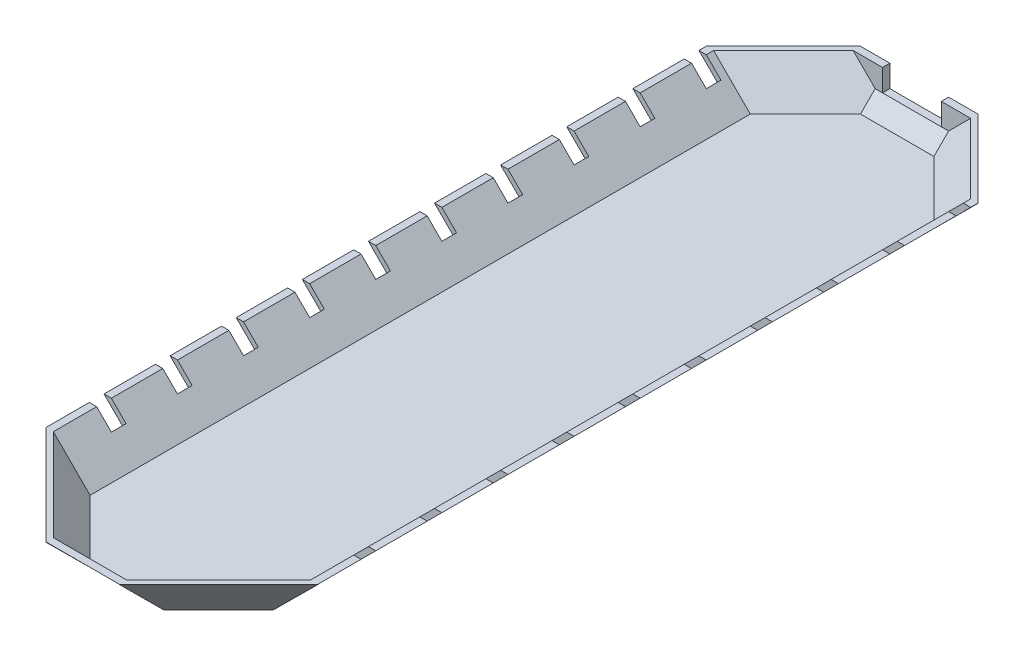
SolidWorks part; units mm, degrees
ref_plane "Front Plane" through (0, 0, 0) normal (0, 0, 1) x (1, 0, 0)
ref_plane "Top Plane" through (0, 0, 0) normal (0, 1, 0) x (1, 0, 0)
ref_plane "Right Plane" through (0, 0, 0) normal (1, 0, 0) x (0, 0, -1)
sketch "Sketch1" plane through (0, 0, 0) normal (0, 1, 0) x (1, 0, 0)
  line L0 (0, -262.2479) -> (0, 262.2479) construction
  line L2 (62.4979, -224.75) -> (62.4979, 224.75)
  line L4 (-62.4979, -224.75) -> (-62.4979, 224.75)
  line L5 (62.4979, -224.75) -> (-62.4979, 224.75) construction
  line L6 (62.4979, 224.75) -> (-62.4979, -224.75) construction
  line L7 (-25, 262.2479) -> (25, 262.2479)
  line L8 (-25, -262.2479) -> (25, -262.2479)
  line L9 (-62.4979, 224.75) -> (-25, 262.2479)
  line L10 (25, 262.2479) -> (62.4979, 224.75)
  line L11 (25, -262.2479) -> (62.4979, -224.75)
  line L12 (-62.4979, -224.75) -> (-25, -262.2479)
  point P0 (0, 0)
  dimension "D1" = 449.5
  dimension "D2" = 50
  dimension "D3" = 25
  dimension "D4" = 50
  dimension "D5" = 25
  dimension "D6" = 53.03
  dimension "D8" = 53.03
extrude "Boss-Extrude1" add sketch "Sketch1" along normal blind 5
sketch "Sketch2" plane through (62.4979, 0, 0) normal (1, 0, 0) x (0, 0, -1)
  line L0 (0, 5) -> (0, 0) construction
  line L1 (-224.75, 5) -> (224.75, 5) construction
ref_plane "Plane1" through (0, 0, 0) normal (0, 0, 1) x (0, -1, 0)
sketch "Sketch3" plane through (0, 0, 0) normal (0, 0, 1) x (0, -1, 0)
  line L0 (0, 62.4979) -> (-5, 62.4979)
  line L1 (-5, 62.4979) -> (-30, 87.4979)
  line L2 (-30, 87.4979) -> (-30, 92.4979)
  line L3 (-30, 92.4979) -> (0, 62.4979)
  line L4 (-5, 62.4979) -> (-30, 62.4979) construction
  line L5 (-30, 62.4979) -> (-30, 87.4979) construction
  line L6 (0, 0) -> (-58.1872, 0) construction
  line L7 (-30, -87.4979) -> (-30, -92.4979)
  line L8 (-5, -62.4979) -> (-30, -87.4979)
  line L9 (0, -62.4979) -> (-5, -62.4979)
  line L10 (-30, -92.4979) -> (0, -62.4979)
  dimension "D1" = 5
  dimension "D2" = 25
extrude "Boss-Extrude2" add sketch "Sketch3" along normal mid plane 449.5
sketch "Sketch5" plane through (0, 0, 262.2479) normal (0, 0, 1) x (1, 0, 0)
  line L0 (0, 5) -> (0, 0) construction
  line L1 (-25, 5) -> (25, 5) construction
ref_plane "Plane2" through (0, 0, 0) normal (-1, 0, 0) x (0, -1, 0)
sketch "Sketch6" plane through (0, 0, 0) normal (-1, 0, 0) x (0, -1, 0)
  line L0 (0, 262.2479) -> (-30, 292.2479)
  line L1 (-30, 292.2479) -> (-30, 287.2479)
  line L2 (-30, 287.2479) -> (-5, 262.2479)
  line L3 (-5, 262.2479) -> (0, 262.2479)
  line L4 (-5, 262.2479) -> (-30, 262.2479) construction
  line L5 (-30, 262.2479) -> (-30, 287.2479) construction
  line L6 (-5, -262.2479) -> (-15, -262.2479) construction
  line L7 (0, -262.2479) -> (-15, -277.2479)
  line L8 (-15, -277.2479) -> (-15, -272.2479)
  line L9 (-15, -272.2479) -> (-5, -262.2479)
  line L10 (-5, -262.2479) -> (0, -262.2479)
  line L11 (-15, -262.2479) -> (-15, -272.2479) construction
  dimension "D1" = 25
  dimension "D2" = 5
  dimension "D3" = 10
  dimension "D4" = 5
extrude "Boss-Extrude3" add sketch "Sketch6" along normal mid plane 50
sketch "Sketch7" plane through (0, 15, 0) normal (0, 1, 0) x (1, 0, 0)
  line L0 (-25, 272.2479) -> (25, 272.2479) construction
  line L1 (-25, 277.2479) -> (-20, 277.2479)
  line L2 (-25, 277.2479) -> (-25, 272.2479)
  line L3 (-25, 272.2479) -> (-20, 272.2479)
  line L4 (-20, 277.2479) -> (-20, 272.2479)
  line L6 (25, 277.2479) -> (20, 277.2479)
  line L7 (25, 277.2479) -> (25, 272.2479)
  line L8 (25, 272.2479) -> (20, 272.2479)
  line L9 (20, 277.2479) -> (20, 272.2479)
  dimension "D1" = 5
  dimension "D2" = 5
extrude "Boss-Extrude5" add sketch "Sketch7" along normal blind 15
sketch "Sketch9" plane through (-143.6239, 0, -143.6239) normal (-0.7071, 0, -0.7071) x (-0.7071, 0, 0.7071)
  line L0 (-141.2446, 5) -> (-141.2446, 0) construction
  line L1 (-167.7596, 5) -> (-114.7296, 5) construction
  line L2 (-167.7596, 0) -> (-114.7296, 0) construction
ref_plane "Plane3" through (99.875, 0, -99.875) normal (0.7071, 0, -0.7071) x (0, -1, 0)
sketch "Sketch10" plane through (99.875, 0, -99.875) normal (0.7071, 0, -0.7071) x (0, -1, 0)
  line L0 (0, 203.1149) -> (-30, 224.3281)
  line L1 (-30, 224.3281) -> (-30, 220.7926)
  line L2 (-30, 220.7926) -> (-5, 203.1149)
  line L3 (-5, 203.1149) -> (0, 203.1149) construction
  line L4 (-5, 203.1149) -> (0, 203.1149)
extrude "Boss-Extrude6" add sketch "Sketch10" along normal mid plane 100
sketch "Sketch11" plane through (143.6239, 0, -143.6239) normal (0.7071, 0, -0.7071) x (-0.7071, 0, -0.7071)
  line L0 (141.2446, 5) -> (141.2446, 0) construction
  line L1 (114.7296, 5) -> (167.7596, 5) construction
  line L2 (114.7296, 0) -> (167.7596, 0) construction
ref_plane "Plane4" through (-99.875, 0, -99.875) normal (0.7071, 0, 0.7071) x (0, -1, 0)
sketch "Sketch13" plane through (-99.875, 0, -99.875) normal (0.7071, 0, 0.7071) x (0, -1, 0)
  line L0 (-5, 203.1149) -> (-30, 220.7926)
  line L1 (-5, 203.1149) -> (0, 203.1149) construction
  line L2 (-30, -93.5164) -> (-30, 224.3281) construction
  line L3 (-30, 220.7926) -> (-30, 224.3281)
  line L4 (-30, 224.3281) -> (0, 203.1149)
  line L5 (0, 203.1149) -> (-5, 203.1149)
  dimension "D1" = 5
extrude "Boss-Extrude7" add sketch "Sketch13" along normal mid plane 96
sketch "Sketch14" plane through (143.6239, 0, 143.6239) normal (0.7071, 0, 0.7071) x (0.7071, 0, -0.7071)
  line L0 (-141.2446, 5) -> (-141.2446, 0) construction
  line L1 (-167.7596, 5) -> (-114.7296, 5) construction
  line L2 (-167.7596, 0) -> (-114.7296, 0) construction
ref_plane "Plane5" through (-99.875, 0, 99.875) normal (-0.7071, 0, 0.7071) x (0, -1, 0)
sketch "Sketch15" plane through (-99.875, 0, 99.875) normal (-0.7071, 0, 0.7071) x (0, -1, 0)
  line L0 (-5, 203.1149) -> (-30, 220.7926)
  line L1 (-5, 203.1149) -> (0, 203.1149) construction
  line L2 (-30, 188.9728) -> (-30, 224.3281) construction
  line L3 (-30, 220.7926) -> (-30, 224.3281)
  line L4 (-30, 224.3281) -> (0, 203.1149)
  line L5 (0, 203.1149) -> (-5, 203.1149)
  dimension "D1" = 5
extrude "Boss-Extrude8" add sketch "Sketch15" along normal mid plane 96
sketch "Sketch16" plane through (-143.6239, 0, 143.6239) normal (-0.7071, 0, 0.7071) x (0.7071, 0, 0.7071)
  line L0 (141.2446, 5) -> (141.2446, 0) construction
  line L1 (114.7296, 5) -> (167.7596, 5) construction
  line L2 (114.7296, 0) -> (167.7596, 0) construction
ref_plane "Plane6" through (99.875, 0, 99.875) normal (-0.7071, 0, -0.7071) x (0, -1, 0)
sketch "Sketch17" plane through (99.875, 0, 99.875) normal (-0.7071, 0, -0.7071) x (0, -1, 0)
  line L0 (-5, 203.1149) -> (-30, 220.7926)
  line L1 (-5, 203.1149) -> (0, 203.1149) construction
  line L2 (-30, 224.3281) -> (-30, -91.2446) construction
  line L3 (-30, 220.7926) -> (-30, 224.3281)
  line L4 (-30, 224.3281) -> (0, 203.1149)
  line L5 (0, 203.1149) -> (-5, 203.1149)
  dimension "D1" = 5
extrude "Boss-Extrude9" add sketch "Sketch17" along normal mid plane 96
sketch "Sketch18" plane through (0, 0, 0) normal (-1, 0, 0) x (0, -1, 0)
  line L0 (0, 262.2479) -> (-30, 292.4401)
  line L1 (-30, 292.4401) -> (0, 277.4401)
  line L2 (0, 277.4401) -> (0, 262.2479)
extrude "Cut-Extrude1" cut sketch "Sketch18" against normal through all both and the other way through all
sketch "Sketch20" plane through (0, -131.1239, -131.1239) normal (0, -0.7071, -0.7071) x (1, 0, 0)
  line L0 (-25, -185.4372) -> (-25, -236.8972) construction
  line L2 (25, -185.4372) -> (-25, -185.4372)
  line L3 (25, -185.4372) -> (25, -233.5501)
  line L4 (25, -233.5501) -> (-25, -233.5501)
  line L5 (-25, -185.4372) -> (-25, -233.5501)
extrude "Cut-Extrude2" cut sketch "Sketch20" along normal blind 105
sketch "Sketch21" plane through (0, 0, -277.2479) normal (0, 0, -1) x (-1, 0, 0)
  line L5 (20, 15) -> (-53.6788, 15)
  line L6 (-53.6788, 15) -> (-53.6788, 30)
  line L7 (-92.6901, 30) -> (-25, 30) construction
  line L8 (-53.6788, 30) -> (47.5713, 30)
  line L9 (25, 30) -> (94.1043, 30) construction
  line L10 (47.5713, 30) -> (47.5713, 15)
  line L11 (47.5713, 15) -> (20, 15)
extrude "Cut-Extrude3" cut sketch "Sketch21" along normal blind 105
sketch "Sketch22" plane through (0, 0, -277.2479) normal (0, 0, -1) x (-1, 0, 0)
  line L0 (-40, 30) -> (-25, 15)
  line L1 (-25, 15) -> (-20, 15)
  line L2 (-20, 15) -> (-20, 30)
  line L3 (-20, 30) -> (-40, 30)
  line L4 (20, 30) -> (40, 30)
  line L5 (40, 30) -> (25, 15)
  line L6 (25, 15) -> (20, 15)
  line L7 (20, 15) -> (20, 30)
extrude "Boss-Extrude11" add sketch "Sketch22" against normal blind 5
sketch "Sketch23" plane through (0, 0, 0) normal (0, 0, 1) x (0, -1, 0)
  line L0 (0, 62.4979) -> (-30, 92.6901)
  line L1 (-30, 92.6901) -> (0, 77.6901)
  line L2 (0, 77.6901) -> (0, 62.4979)
extrude "Cut-Extrude4" cut sketch "Sketch23" against normal through all both and the other way through all
sketch "Sketch24" plane through (-31.2489, -31.2489, 0) normal (-0.7071, -0.7071, 0) x (0, 0, 1)
  line L0 (-224.75, 44.1927) -> (-259.6143, 44.1927)
  line L1 (-259.6143, 44.1927) -> (-259.6143, 90.2059)
  line L2 (-259.6143, 90.2059) -> (275.9375, 90.2059)
  line L3 (275.9375, 90.2059) -> (275.9375, 44.1927)
  line L4 (275.9375, 44.1927) -> (-224.75, 44.1927)
extrude "Cut-Extrude5" cut sketch "Sketch24" along normal blind 29
sketch "Sketch25" plane through (0, 5, 0) normal (0, 1, 0) x (1, 0, 0)
  line L0 (62.4979, -224.75) -> (62.4979, -195.25)
  line L1 (62.4979, -224.75) -> (62.4979, 224.75) construction
  line L2 (62.4979, -195.25) -> (92.4979, -195.25) construction
  line L3 (92.4979, -224.3656) -> (92.4979, 224.3656) construction
  line L4 (0, -292.2479) -> (0, -143.3871) construction
  line L5 (92.4979, -195.25) -> (77.4979, -195.25)
  line L6 (92.4979, -195.25) -> (92.4979, -185.25)
  line L7 (92.4979, -185.25) -> (77.4979, -185.25)
  line L8 (77.4979, -195.25) -> (77.4979, -185.25)
  line L9 (-24.6156, -292.2479) -> (24.6156, -292.2479) construction
  line L10 (-92.4979, -195.25) -> (-92.4979, -185.25)
  line L11 (-92.4979, -185.25) -> (-77.4979, -185.25)
  line L12 (-77.4979, -195.25) -> (-77.4979, -185.25)
  line L13 (-92.4979, -195.25) -> (-77.4979, -195.25)
  line L14 (92.4979, -150.25) -> (92.4979, -140.25)
  line L15 (92.4979, -150.25) -> (77.4979, -150.25)
  line L16 (77.4979, -150.25) -> (77.4979, -140.25)
  line L17 (92.4979, -140.25) -> (77.4979, -140.25)
  line L18 (-92.4979, -150.25) -> (-92.4979, -140.25)
  line L19 (-92.4979, -140.25) -> (-77.4979, -140.25)
  line L20 (-77.4979, -150.25) -> (-77.4979, -140.25)
  line L21 (-92.4979, -150.25) -> (-77.4979, -150.25)
  line L22 (92.4979, -105.25) -> (92.4979, -95.25)
  line L23 (92.4979, -105.25) -> (77.4979, -105.25)
  line L24 (77.4979, -105.25) -> (77.4979, -95.25)
  line L25 (92.4979, -95.25) -> (77.4979, -95.25)
  line L26 (-92.4979, -105.25) -> (-92.4979, -95.25)
  line L27 (-92.4979, -95.25) -> (-77.4979, -95.25)
  line L28 (-77.4979, -105.25) -> (-77.4979, -95.25)
  line L29 (-92.4979, -105.25) -> (-77.4979, -105.25)
  line L30 (92.4979, -60.25) -> (92.4979, -50.25)
  line L31 (92.4979, -60.25) -> (77.4979, -60.25)
  line L32 (77.4979, -60.25) -> (77.4979, -50.25)
  line L33 (92.4979, -50.25) -> (77.4979, -50.25)
  line L34 (-92.4979, -60.25) -> (-92.4979, -50.25)
  line L35 (-92.4979, -50.25) -> (-77.4979, -50.25)
  line L36 (-77.4979, -60.25) -> (-77.4979, -50.25)
  line L37 (-92.4979, -60.25) -> (-77.4979, -60.25)
  line L38 (92.4979, -15.25) -> (92.4979, -5.25)
  line L39 (92.4979, -15.25) -> (77.4979, -15.25)
  line L40 (77.4979, -15.25) -> (77.4979, -5.25)
  line L41 (92.4979, -5.25) -> (77.4979, -5.25)
  line L42 (-92.4979, -15.25) -> (-92.4979, -5.25)
  line L43 (-92.4979, -5.25) -> (-77.4979, -5.25)
  line L44 (-77.4979, -15.25) -> (-77.4979, -5.25)
  line L45 (-92.4979, -15.25) -> (-77.4979, -15.25)
  line L46 (92.4979, 29.75) -> (92.4979, 39.75)
  line L47 (92.4979, 29.75) -> (77.4979, 29.75)
  line L48 (77.4979, 29.75) -> (77.4979, 39.75)
  line L49 (92.4979, 39.75) -> (77.4979, 39.75)
  line L50 (-92.4979, 29.75) -> (-92.4979, 39.75)
  line L51 (-92.4979, 39.75) -> (-77.4979, 39.75)
  line L52 (-77.4979, 29.75) -> (-77.4979, 39.75)
  line L53 (-92.4979, 29.75) -> (-77.4979, 29.75)
  line L54 (92.4979, 74.75) -> (92.4979, 84.75)
  line L55 (92.4979, 74.75) -> (77.4979, 74.75)
  line L56 (77.4979, 74.75) -> (77.4979, 84.75)
  line L57 (92.4979, 84.75) -> (77.4979, 84.75)
  line L58 (-92.4979, 74.75) -> (-92.4979, 84.75)
  line L59 (-92.4979, 84.75) -> (-77.4979, 84.75)
  line L60 (-77.4979, 74.75) -> (-77.4979, 84.75)
  line L61 (-92.4979, 74.75) -> (-77.4979, 74.75)
  line L62 (92.4979, 119.75) -> (92.4979, 129.75)
  line L63 (92.4979, 119.75) -> (77.4979, 119.75)
  line L64 (77.4979, 119.75) -> (77.4979, 129.75)
  line L65 (92.4979, 129.75) -> (77.4979, 129.75)
  line L66 (-92.4979, 119.75) -> (-92.4979, 129.75)
  line L67 (-92.4979, 129.75) -> (-77.4979, 129.75)
  line L68 (-77.4979, 119.75) -> (-77.4979, 129.75)
  line L69 (-92.4979, 119.75) -> (-77.4979, 119.75)
  line L70 (92.4979, 164.75) -> (92.4979, 174.75)
  line L71 (92.4979, 164.75) -> (77.4979, 164.75)
  line L72 (77.4979, 164.75) -> (77.4979, 174.75)
  line L73 (92.4979, 174.75) -> (77.4979, 174.75)
  line L74 (-92.4979, 164.75) -> (-92.4979, 174.75)
  line L75 (-92.4979, 174.75) -> (-77.4979, 174.75)
  line L76 (-77.4979, 164.75) -> (-77.4979, 174.75)
  line L77 (-92.4979, 164.75) -> (-77.4979, 164.75)
  line L78 (92.4979, 209.75) -> (92.4979, 219.75)
  line L79 (92.4979, 209.75) -> (77.4979, 209.75)
  line L80 (77.4979, 209.75) -> (77.4979, 219.75)
  line L81 (92.4979, 219.75) -> (77.4979, 219.75)
  line L82 (-92.4979, 209.75) -> (-92.4979, 219.75)
  line L83 (-92.4979, 219.75) -> (-77.4979, 219.75)
  line L84 (-77.4979, 209.75) -> (-77.4979, 219.75)
  line L85 (-92.4979, 209.75) -> (-77.4979, 209.75)
  dimension "D1" = 29.5
  dimension "D2" = 10
  dimension "D3" = 15
  dimension "D4" = 10
extrude "Cut-Extrude6" cut sketch "Sketch25" against normal through all both and the other way through all contours L78 L81 L80 L79 | L70 L73 L72 L71 | L62 L65 L64 L63 | L54 L57 L56 L55 | L46 L49 L48 L47 | L38 L41 L40 L39 | L30 L33 L32 L31 | L8 L5 L6 L7 | L14 L17 L16 L15 | L22 L25 L24 L23 | L10 L13 L12 L11 | L18 L21 L20 L19 | L26 L29 L28 L27 | L34 L37 L36 L35 | L50 L53 L52 L51 | L82 L85 L84 L83 | L74 L77 L76 L75 | L66 L69 L68 L67 | L58 L61 L60 L59 | L45 L44 L43 L42
